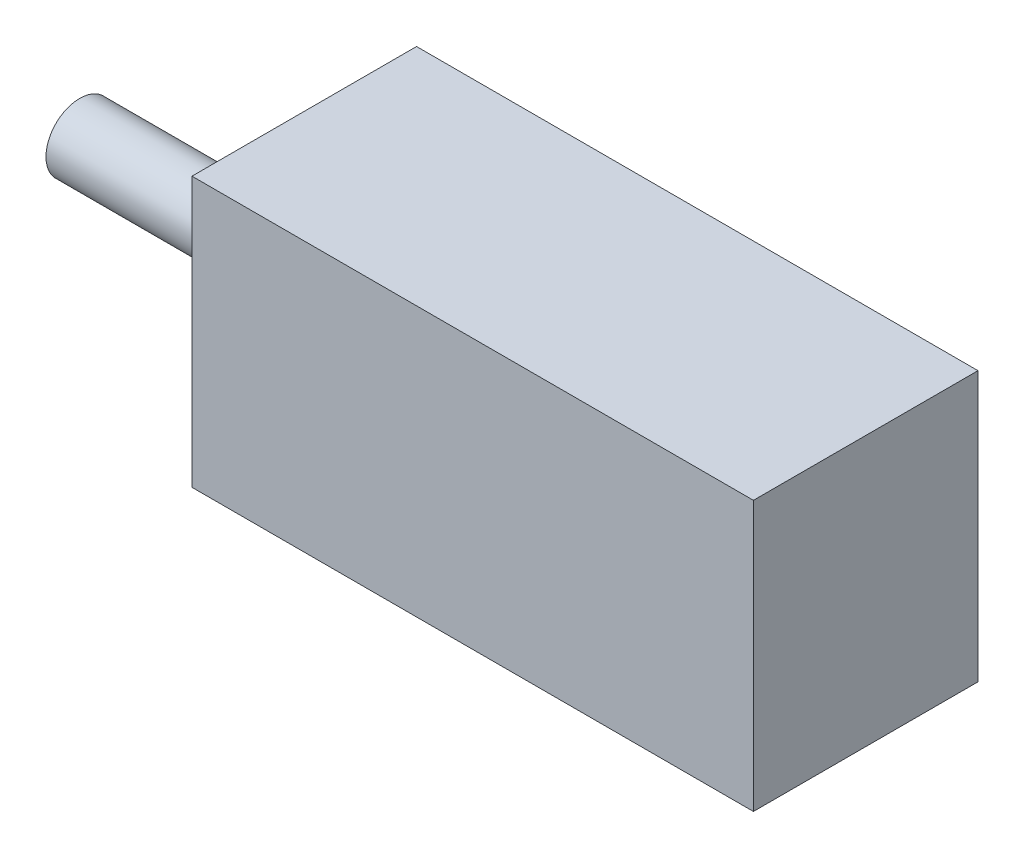
SolidWorks part; units mm, degrees
ref_plane "Front Plane" through (0, 0, 0) normal (0, 0, 1) x (1, 0, 0)
ref_plane "Top Plane" through (0, 0, 0) normal (0, 1, 0) x (1, 0, 0)
ref_plane "Right Plane" through (0, 0, 0) normal (1, 0, 0) x (0, 0, -1)
sketch "Sketch1" plane through (0, 0, 0) normal (0, 1, 0) x (1, 0, 0)
  line L1 (-1.3095, 0.506) -> (23.6905, 0.506)
  line L2 (-1.3095, 0.506) -> (-1.3095, -9.494)
  line L3 (-1.3095, -9.494) -> (23.6905, -9.494)
  line L4 (23.6905, 0.506) -> (23.6905, -9.494)
  dimension "D1" = 10
  dimension "D2" = 25
extrude "Boss-Extrude1" add sketch "Sketch1" along normal blind 12
sketch "Sketch2" plane through (-1.3095, 0, 0) normal (-1, 0, 0) x (0, 0, 1)
  line L0 (-0.506, 12) -> (9.494, 12) construction
  line L2 (-0.506, 12) -> (-0.506, 0) construction
  circle A0 centre (4.494, 6) radius 1.5
  point P2 (4.494, 12)
  point P7 (7.9684, 0)
  dimension "D1" = 3
  dimension "D2" = 6
  dimension "D3" = 5
extrude "Boss-Extrude2" add sketch "Sketch2" along normal blind 10
equation "\"ๅ\"=33.0613"
